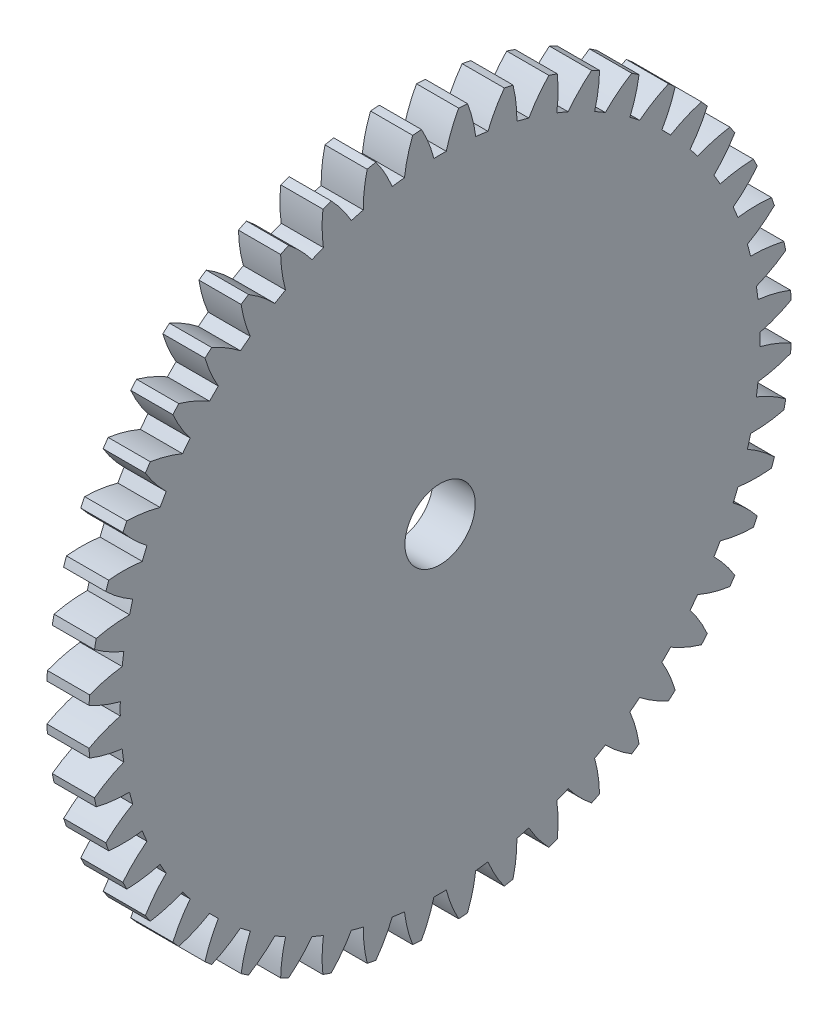
SolidWorks part; units mm, degrees
ref_plane "Plane1" through (0, 0, 0) normal (0, 0, 1) x (1, 0, 0)
ref_plane "Plane2" through (0, 0, 0) normal (0, 1, 0) x (1, 0, 0)
ref_plane "Plane3" through (0, 0, 0) normal (1, 0, 0) x (0, 0, -1)
sketch "HoldingSke" plane through (0, 0, 0) normal (0, 1, 0) x (1, 0, 0)
  line L0 (0, 0) -> (0.6691, -0.7431)
  line L1 (-15, 0) -> (100, 0) construction
  line L2 (0, 0) -> (-2.1039, 2.3779)
  line L3 (0, 0) -> (-11.863, 4.5341)
  line L4 (0, 0) -> (5.7786, 6.4178)
  line L5 (0, 0) -> (-46.8476, -17.4728)
  line L6 (0, 0) -> (-2.4869, -1.6779)
  line L7 (-2.1039, 2.3779) -> (8.6586, 51.2059)
  line L8 (-76.2, 54.61) -> (-75.3, 54.61)
  line L9 (-71.009, 38.7566) -> (-53.1078, 45.2721)
  line L10 (-76.2, 71.12) -> (104.1128, 71.12)
  line L11 (0, 0) -> (-3, 0)
  line L12 (-76.2, 101.6) -> (-76.162, 101.6)
  line L13 (24.9733, 27.94) -> (52.9518, 28.4284)
  line L14 (24.9733, 27.94) -> (24.9743, 27.94)
  line L15 (24.9733, 27.94) -> (100.4006, 29.5858)
  line L16 (-63.627, -1) -> (-12.827, -1)
  circle A0 centre (0, 0) radius 2.5
  circle A1 centre (0, 0) radius 22.749
  circle A2 centre (0, 0) radius 37.5
  circle A3 centre (0, 0) radius 2.5
  dimension "MHD" = 45.498
  dimension "Hub_dia" = 75
  dimension "Bore" = 5
  dimension "MBD" = 5
  dimension "Num_teeth" = 48
  dimension "Pitch_radius" = 180.3128
  dimension "Pitch" = 1
  dimension "Width" = 3
  dimension "Overall_len" = 50
  dimension "Show_teeth" = 48
  dimension "Thickness" = 3
  dimension "OAL" = 50.0001
  dimension "T_dim" = 0.9
  dimension "Ap" = 20
  dimension "H" = 19.05
  dimension "Backlash" = 0.038
  dimension "Addendum_fac" = 1
  dimension "Dedendum_fac" = 1.25
  dimension "Clearance_fac" = 0.25
  dimension "Dedendum_add" = 0.001
  dimension "Module" = 1
sketch "BasProSke" plane through (0, 0, 0) normal (0, 1, 0) x (1, 0, 0)
  line L0 (-10, 0) -> (60, 0) construction
  line L1 (0, 0) -> (0, 25)
  line L2 (0, 0) -> (3, 0)
  line L3 (3, 0) -> (3, 25)
  line L4 (3, 25) -> (0, 25)
  dimension "Diameter" = 50
  dimension "Thickness" = 3
revolve "Base-Revolve" add sketch "BasProSke" angle 360 about L0
sketch "TooCutSke" plane through (0, 0, 0) normal (1, 0, 0) x (0, 0, -1)
  line L1 (0, 0) -> (0, 107) construction
  line L2 (0, 0) -> (-0.8518, 23.9849) construction
  line L3 (0, 0) -> (-3.1379, 47.8757) construction
  line L4 (-0.8518, 23.9849) -> (-1.569, 23.9379) construction
  arc A0 (0.4395, 22.7448) -> (-0.4395, 22.7448) centre (0, 0) ccw
  arc A1 (1.3336, 24.9898) -> (-1.3336, 24.9898) centre (0, 0) ccw
  circle A2 centre (0, 0) radius 24 construction
  circle A3 centre (0, 0) radius 22.5526 construction
  arc A4 (-0.4395, 22.7448) -> (-1.3336, 24.9898) centre (-9.7344, 20.3436) ccw
  arc A5 (1.3336, 24.9898) -> (0.4395, 22.7448) centre (9.7344, 20.3436) ccw
  dimension "Root_dia" = 45.498
  dimension "Overcut_dia" = 50.0508
  dimension "Pitch_dia" = 48
  dimension "Base_dia" = 45.1052
  dimension "Flank_rad" = 9.6
  dimension "Half_ang" = 3.75
  dimension "Half_CT" = 0.7188
extrude "ToothCut" cut sketch "TooCutSke" along normal through all
fillet "Breaks" [suppressed] radius 0.02
fillet "RootFillets" [suppressed] radius 0.251
pattern_circular "TeethCuts" count 48 every 7.5 about axis through (-10, 0, 0) along (1, 0, 0) of "ToothCut", "RootFillets", "Breaks"
sketch "HubNeaOneSke" plane through (0, 0, 0) normal (-1, 0, 0) x (0, 0, 1)
  circle A0 centre (0, 0) radius 22.749
  dimension "Diameter" = 45.498
extrude "HubNearOne" [suppressed] add sketch "HubNeaOneSke" along normal blind 47.0001
sketch "HubNeaBotSke" plane through (0, 0, 0) normal (-1, 0, 0) x (0, 0, 1)
  circle A0 centre (0, 0) radius 22.749
  dimension "Diameter" = 45.498
extrude "HubNearBoth" [suppressed] add sketch "HubNeaBotSke" along normal blind 23.5
ref_plane "FarPln" through (3, 0, 0) normal (1, 0, 0) x (0, 0, -1)
sketch "HubFarSke" plane through (3, 0, 0) normal (1, 0, 0) x (0, 0, -1)
  circle A0 centre (0, 0) radius 22.749
  dimension "Diameter" = 45.498
extrude "HubFar" [suppressed] add sketch "HubFarSke" along normal blind 23.5
sketch "BorSke" plane through (0, 0, 0) normal (1, 0, 0) x (0, 0, -1)
  circle A0 centre (0, 0) radius 2.5
  dimension "Diameter" = 5
extrude "Bore" cut sketch "BorSke" along normal mid plane 100.0001
sketch "KeySke" plane through (0, 0, 0) normal (1, 0, 0) x (0, 0, -1)
  line L0 (-1, 0) -> (-1, 3.4)
  line L1 (-1, 3.4) -> (1, 3.4)
  line L2 (1, 3.4) -> (1, 0)
  line L3 (0, 0) -> (0, 34) construction
  line L4 (-1, 0) -> (1, 0)
  dimension "Offset" = 3.4
  dimension "Width" = 2
extrude "Keyway" [suppressed] cut sketch "KeySke" along normal mid plane 100.0001
pattern_circular "Keyway2" [suppressed] count 2 every 90 about axis through (-10, 0, 0) along (1, 0, 0)
equation "' \"Module@HoldingSke\" = 6.35"
equation "' \"Num_teeth@HoldingSke\" = 12"
equation "' \"Ap@HoldingSke\" =  20"
equation "' \"Width@HoldingSke\" = 0.5 * 25.4"
equation "' \"Hub_dia@HoldingSke\"= 1 * 25.4"
equation "' \"Overall_len@HoldingSke\" = 1.0 * 25.4"
equation "' \"Bore@HoldingSke\" = 0.75 * 25.4"
equation "' \"T_dim@HoldingSke\" = 0.1 * 25.4"
equation "' \"Width@KeySke\" = 0.25 * 25.4"
equation "' \"Show_teeth@HoldingSke\" = 13"
equation "' \"Backlash@HoldingSke\" = 0.009 * 25.4"
equation "' \"Addendum_fac@HoldingSke\" = 1.0"
equation "' \"Dedendum_fac@HoldingSke\" = 1.25"
equation "' \"Dedendum_add@HoldingSke\" = 0.00005 * 25.4"
equation "' \"Clearance_fac@HoldingSke\" = 0.25"
equation "\"Pitch@HoldingSke\" = 1 / \"Module@HoldingSke\""
equation "\"Overcut_dia@TooCutSke\" = (\"Num_teeth@HoldingSke\" + 2 * \"Addendum_fac@HoldingSke\") / \"Pitch@HoldingSke\" + 0.002 * 25.4"
equation "\"Pitch_dia@TooCutSke\" = \"Num_teeth@HoldingSke\" / \"Pitch@HoldingSke\""
equation "\"Base_dia@TooCutSke\" = \"Num_teeth@HoldingSke\" / \"Pitch@HoldingSke\" * cos((\"Ap@HoldingSke\"  * 3.14159265 / 180))"
equation "\"Root_dia@TooCutSke\" = (\"Num_teeth@HoldingSke\" + 2) / \"Pitch@HoldingSke\" - 2 * (\"Addendum_fac@HoldingSke\" + \"Dedendum_fac@HoldingSke\") / \"Pitch@HoldingSke\" - \"Dedendum_add@HoldingSke\" * 2"
equation "\"Half_ang@TooCutSke\" = 180 / \"Num_teeth@HoldingSke\""
equation "\"Half_CT@TooCutSke\" = \"Num_teeth@HoldingSke\" / \"Pitch@HoldingSke\" * sin((3.14159265 / 2 / \"Num_teeth@HoldingSke\")) / 2 - 7 * \"Backlash@HoldingSke\" / 4"
equation "\"Flank_rad@TooCutSke\" = \"Num_teeth@HoldingSke\" / \"Pitch@HoldingSke\" / 5"
equation "\"Radius@RootFillets\" = \"Clearance_fac@HoldingSke\" / \"Pitch@HoldingSke\" + \"Dedendum_add@HoldingSke\""
equation "\"Break_rad@Breaks\" = 0.02 / \"Pitch@HoldingSke\""
equation "\"Thickness@HoldingSke\" = \"Width@HoldingSke\""
equation "\"OAL@HoldingSke\" = \"Thickness@HoldingSke\""
equation "\"MHD@HoldingSke\" = (\"Num_teeth@HoldingSke\" + 2) / \"Pitch@HoldingSke\" - 2 * (\"Addendum_fac@HoldingSke\" + \"Dedendum_fac@HoldingSke\")  / \"Pitch@HoldingSke\" - \"Dedendum_add@HoldingSke\" * 2"
equation "\"MBD@HoldingSke\" = (\"Num_teeth@HoldingSke\" + 2) / \"Pitch@HoldingSke\" - 2 * (\"Addendum_fac@HoldingSke\" + \"Dedendum_fac@HoldingSke\")  / \"Pitch@HoldingSke\" - \"Dedendum_add@HoldingSke\" * 2 - 0.002 * 25.4"
equation "\"MHD@HoldingSke\" = ((sgn( \"MHD@HoldingSke\" - \"Hub_dia@HoldingSke\" )-1)*( \"MHD@HoldingSke\" - \"Hub_dia@HoldingSke\" ))/-2+ \"Hub_dia@HoldingSke\""
equation "\"MBD@HoldingSke\" = ((sgn( \"MBD@HoldingSke\" - \"Bore@HoldingSke\" )-1)*( \"MBD@HoldingSke\" - \"Bore@HoldingSke\" ))/-2+ \"Bore@HoldingSke\""
equation "\"OAL@HoldingSke\" = ((sgn( \"OAL@HoldingSke\" - \"Overall_len@HoldingSke\" )+1)*( \"OAL@HoldingSke\" - \"Overall_len@HoldingSke\" ))/2 + \"Overall_len@HoldingSke\" + 0.000002 * 25.4"
equation "\"Num_teeth@TeethCuts\" = int( \"Show_teeth@HoldingSke\" ) + 1"
equation "\"Num_teeth@TeethCuts\" = ((sgn( \"Num_teeth@TeethCuts\" - \"Num_teeth@HoldingSke\" )-1)*( \"Num_teeth@TeethCuts\" - \"Num_teeth@HoldingSke\" ))/-2+ \"Num_teeth@HoldingSke\""
equation "\"Num_teeth@TeethCuts\" = ((sgn( \"Num_teeth@TeethCuts\" - 2.0)+1)*( \"Num_teeth@TeethCuts\" - 2.0))/2 +2.0"
equation "\"Angle@TeethCuts\" = 360.0 / \"Num_teeth@HoldingSke\""
equation "\"Diameter@BasProSke\" = (\"Num_teeth@HoldingSke\" + 2 * \"Addendum_fac@HoldingSke\") / \"Pitch@HoldingSke\""
equation "\"Thickness@BasProSke\"  = \"Thickness@HoldingSke\""
equation "' \"Fillet_rad@BasProSke\" =  \"Thickness@HoldingSke\" * 0.05"
equation "\"MHD@HoldingSke\" = ((sgn( \"MHD@HoldingSke\" - \"Root_dia@TooCutSke\" )-1)*( \"MHD@HoldingSke\" - \"Root_dia@TooCutSke\" ))/-2+ \"Root_dia@TooCutSke\""
equation "\"Diameter@HubNeaOneSke\" = \"MHD@HoldingSke\""
equation "\"Length@HubNearOne\" = \"OAL@HoldingSke\" - \"Thickness@BasProSke\""
equation "\"Diameter@HubNeaBotSke\" = \"MHD@HoldingSke\""
equation "\"Length@HubNearBoth\" = ( \"OAL@HoldingSke\" - \"Thickness@BasProSke\" ) / 2.0"
equation "\"Thickness@FarPln\" = \"Thickness@BasProSke\""
equation "\"Diameter@HubFarSke\" = \"MHD@HoldingSke\""
equation "\"Length@HubFar\" = ( \"OAL@HoldingSke\" - \"Thickness@BasProSke\" ) / 2.0"
equation "\"Diameter@BorSke\" = \"MBD@HoldingSke\""
equation "\"D1@Bore\" = \"OAL@HoldingSke\" * 2.0"
equation "\"D1@Keyway\" = \"OAL@HoldingSke\" * 2.0"
equation "\"Offset@KeySke\" = \"T_dim@HoldingSke\" + \"MBD@HoldingSke\" / 2.0"
